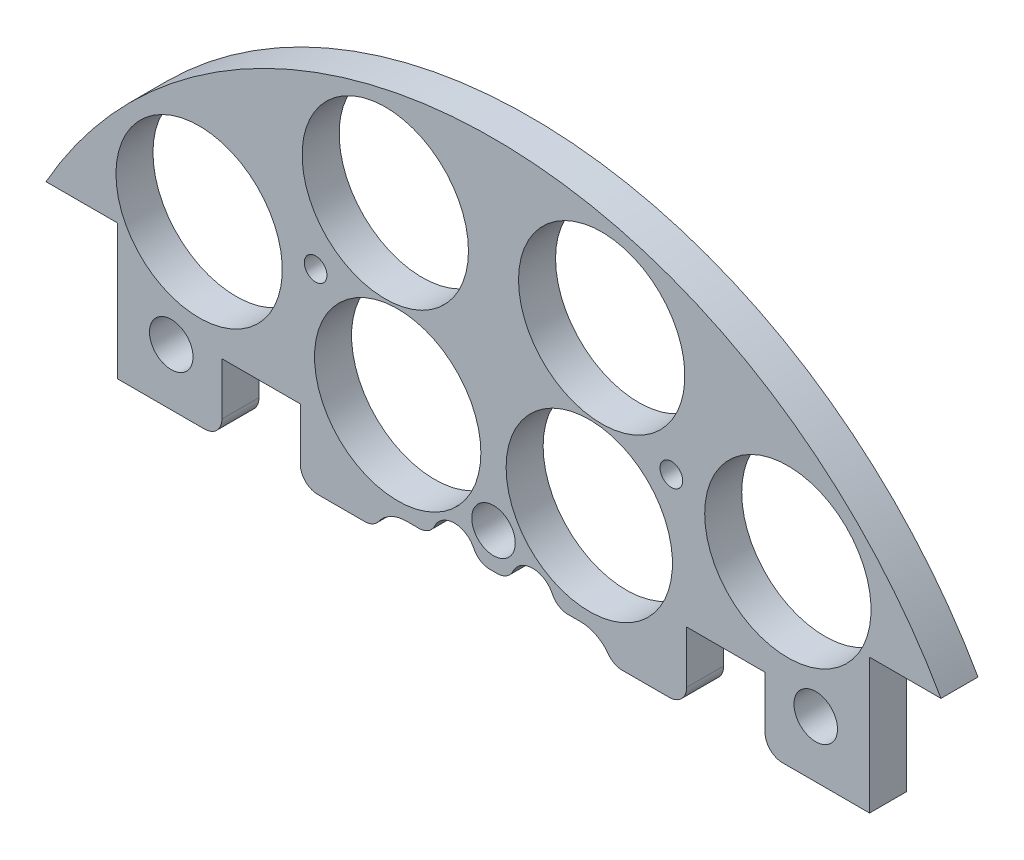
SolidWorks part; units mm, degrees
ref_plane "Front Plane" through (0, 0, 0) normal (0, 0, 1) x (1, 0, 0)
ref_plane "Top Plane" through (0, 0, 0) normal (0, 1, 0) x (1, 0, 0)
ref_plane "Right Plane" through (0, 0, 0) normal (1, 0, 0) x (0, 0, -1)
sketch "Sketch1" plane through (0, 0, 0) normal (0, 0, 1) x (1, 0, 0)
  line L0 (0, 0) -> (-82.1241, 0) construction
  line L1 (0, 0) -> (0, 95.6219) construction
  line L3 (-65.2538, 36.83) -> (-54.8398, 36.83)
  line L5 (-65.2538, -36.83) -> (-54.8398, -36.83)
  line L6 (-54.8398, 36.83) -> (-54.8398, -36.83)
  line L7 (65.2538, -36.83) -> (54.8398, -36.83)
  line L8 (65.2538, 36.83) -> (54.8398, 36.83)
  line L9 (54.8398, 36.83) -> (54.8398, -36.83)
  arc A0 (-65.2538, -36.83) -> (65.2538, -36.83) centre (0, 0) ccw
  circle A1 centre (-45.466, 11.049) radius 1.651
  circle A2 centre (-20.0673, 10.795) radius 1.651
  circle A3 centre (-20.0673, -10.795) radius 1.651
  circle A4 centre (-45.466, -11.049) radius 1.651
  circle A5 centre (45.466, -11.049) radius 1.651
  circle A6 centre (20.0673, -10.795) radius 1.651
  circle A7 centre (20.0673, 10.795) radius 1.651
  circle A8 centre (45.466, 11.049) radius 1.651
  arc A9 (65.2538, 36.83) -> (-65.2538, 36.83) centre (0, 0) ccw
  dimension "D2" = 3.302
  dimension "D3" = 3.302
  dimension "D4" = 25.4
  dimension "D5" = 10.795
  dimension "D10" = 45.466
  dimension "D6" = 73.66
  dimension "D7" = 10.414
  dimension "D8" = 74.93
  dimension "D9" = 74.93
  dimension "D11" = 36.83
extrude "Boss-Extrude2" add sketch "Sketch1" along normal blind 5.3975
sketch "Sketch2" plane through (0, 0, 5.3975) normal (0, 0, 1) x (1, 0, 0)
  line L0 (0, 68.58) -> (0, 55.88) construction
  line L1 (-9.525, 68.58) -> (9.525, 68.58)
  line L2 (-9.525, 68.58) -> (-9.525, 55.88)
  line L3 (-9.525, 55.88) -> (9.525, 55.88)
  line L4 (9.525, 68.58) -> (9.525, 55.88)
  line L5 (-9.525, 62.23) -> (9.525, 62.23) construction
  arc A0 (65.2538, 36.83) -> (-65.2538, 36.83) centre (0, 0) ccw construction
  circle A1 centre (-20.0673, 10.795) radius 1.651 construction
  circle A2 centre (20.0673, 10.795) radius 1.651 construction
  circle A3 centre (-6.731, 62.23) radius 1.143
  circle A4 centre (6.731, 62.23) radius 1.143
  dimension "D4" = 2.286
  dimension "D5" = 0
  dimension "D6" = 6.731
  dimension "D1" = 19.05
  dimension "D2" = 12.7
  dimension "D3" = 55.88
extrude "Cut-Extrude1" cut sketch "Sketch2" against normal through all contours A3 | A4
sketch "Sketch3" plane through (0, 0, 0) normal (0, 0, -1) x (-1, 0, 0)
  line L0 (0, 0) -> (0, -116.2908) construction
  line L1 (0, 0) -> (-153.8039, 0) construction
  arc A0 (65.2538, 36.83) -> (-65.2538, 36.83) centre (0, 0) ccw construction
  circle A4 centre (-42.926, -42.926) radius 12.1285
  circle A6 centre (13.97, -34.29) radius 12.1285
  circle A7 centre (13.97, 34.29) radius 12.1285
  circle A8 centre (-42.926, 42.926) radius 12.1285
  circle A11 centre (42.926, 42.926) radius 12.1285
  circle A12 centre (-13.97, 34.29) radius 12.1285
  circle A13 centre (-13.97, -34.29) radius 12.1285
  circle A14 centre (42.926, -42.926) radius 12.1285
  point P36 (0, 0)
  point P53 (0, 0)
  point P55 (0, 0)
  dimension "D1" = 42.926
  dimension "D3" = 42.926
  dimension "D4" = 24.257
  dimension "D5" = 34.29
  dimension "D6" = 13.97
extrude "Cut-Extrude2" cut sketch "Sketch3" against normal through all
sketch "Sketch4" plane through (0, 0, 0) normal (0, 0, -1) x (-1, 0, 0)
  line L1 (-15.7702, 56.3138) -> (12.7925, 56.3138)
  line L2 (-15.7702, 56.3138) -> (-15.7702, 67.9913)
  line L3 (-15.7702, 67.9913) -> (12.7925, 67.9913)
  line L4 (12.7925, 56.3138) -> (12.7925, 67.9913)
extrude "Boss-Extrude3" add sketch "Sketch4" against normal up to surface (5.3975 mm away) up to face at (-55.0545, -42.926, 5.3975)
sketch "Sketch5" plane through (0, 0, 0) normal (0, 0, -1) x (-1, 0, 0)
  line L1 (-113.3786, -90.442) -> (117.3207, -90.442)
  line L2 (-113.3786, -90.442) -> (-113.3786, 17.145)
  line L3 (-113.3786, 17.145) -> (117.3207, 17.145)
  line L4 (117.3207, -90.442) -> (117.3207, 17.145)
  circle A1 centre (20.0673, 10.795) radius 1.651 construction
  dimension "D1" = 6.35
extrude "Cut-Extrude3" cut sketch "Sketch5" against normal through all
sketch "Sketch6" plane through (0, 0, 0) normal (0, 0, -1) x (-1, 0, 0)
  line L0 (0, 0) -> (0, 74.93) construction
  line L1 (0, 0) -> (-15.5068, 57.8721) construction
  arc A0 (65.2538, 36.83) -> (-65.2538, 36.83) centre (0, 0) ccw construction
  circle A1 centre (-15.7776, 58.8828) radius 12.1285
  circle A3 centre (15.7776, 58.8828) radius 12.1285
  dimension "D1" = 24.257
  dimension "D2" = 0
  dimension "D4" = 60.96
  dimension "D3" = 15
extrude "Cut-Extrude4" cut sketch "Sketch6" against normal through all
extrude "Cut-Extrude55" cut sketch "Sketch57" against normal through all both and the other way through all
sketch "Sketch57" plane through (-29.8755, 133.1307, 31.75) normal (0, 0, 1) x (0.01, 0.9999, 0)
  line L0 (-132.614, -31.3134) -> (-132.614, 57.8454) construction
  line L1 (-132.614, -31.3134) -> (-222.516, -31.3134) construction
  circle A0 centre (-158.014, 14.4066) radius 3.175
  circle A1 centre (-173.254, -31.3134) radius 3.175
  circle A3 centre (-158.014, -77.0334) radius 3.175
  circle A4 centre (-107.214, -77.0334) radius 3.175
  circle A5 centre (-91.974, -31.3134) radius 3.175
  circle A6 centre (-107.214, 14.4066) radius 3.175
sketch "Sketch58" [suppressed] plane through (0, 0, 0) normal (0, 0, -1) x (-1, 0, 0)
  circle A0 centre (-46.082, 25.1518) radius 4.445
  circle A1 centre (-0.5167, 40.8482) radius 4.445
  circle A2 centre (45.3534, 26.0662) radius 4.445
  circle A3 centre (-46.082, 25.1518) radius 3.175 construction
  circle A4 centre (-0.5167, 40.8482) radius 3.175 construction
  circle A5 centre (45.3534, 26.0662) radius 3.175 construction
  dimension "D1" = 1.27
  dimension "D2" = 1.27
  dimension "D3" = 1.27
extrude "Boss-Extrude4" [suppressed] add sketch "Sketch58" against normal up to surface (6.35 mm away)
extrude "Cut-Extrude56" cut sketch "Sketch59" against normal through all both and the other way through all
sketch "Sketch59" plane through (31.3134, 132.614, -19.05) normal (0, 0, -1) x (0, 1, 0)
  line L0 (-132.614, -31.3134) -> (-132.614, 57.8454) construction
  line L1 (-132.614, -31.3134) -> (-222.516, -31.3134) construction
  circle A0 centre (-158.014, 14.4066) radius 3.175
  circle A1 centre (-173.254, -31.3134) radius 3.175
  circle A3 centre (-158.014, -77.0334) radius 3.175
  circle A4 centre (-107.214, -77.0334) radius 3.175
  circle A5 centre (-91.974, -31.3134) radius 3.175
  circle A6 centre (-107.214, 14.4066) radius 3.175
extrude "Cut-Extrude60" cut sketch "Sketch63" against normal blind 29.21
sketch "Sketch63" plane through (31.3134, 132.559, -15.875) normal (0, 0, -1) x (0, 1, 0)
  line L0 (-132.559, -31.3134) -> (6.1626, -31.3134) construction
  line L2 (-132.559, -31.3134) -> (-132.559, -122.6589) construction
  circle A0 centre (-190.979, 2.9766) radius 1.651
  circle A2 centre (-154.784, -31.3134) radius 1.651
  circle A3 centre (-190.979, -65.6034) radius 1.651
  circle A4 centre (-110.334, -31.3134) radius 1.651
  circle A5 centre (-74.139, -65.6034) radius 1.651
  circle A6 centre (-74.139, 2.9766) radius 1.651
extrude "Cut-Extrude151" cut sketch "Sketch155" against normal blind 29.21
sketch "Sketch155" plane through (-31.3134, 132.559, 15.875) normal (0, 0, 1) x (0, 1, 0)
  line L0 (-143.7712, -34.3645) -> (6.1626, -34.3645) construction
  line L2 (-143.7712, -34.3645) -> (-143.7712, -122.6589) construction
  circle A0 centre (-202.1912, -0.0745) radius 1.651
  circle A2 centre (-165.9962, -34.3645) radius 1.651
  circle A3 centre (-202.1912, -68.6545) radius 1.651
  circle A4 centre (-121.5462, -34.3645) radius 1.651
  circle A5 centre (-85.3512, -68.6545) radius 1.651
  circle A6 centre (-85.3512, -0.0745) radius 1.651
sketch "Sketch156" plane through (0, 0, 0) normal (0, 0, -1) x (-1, 0, 0)
  line L0 (54.8398, 17.145) -> (-54.8398, 17.145) construction
  line L1 (39.5998, 17.145) -> (28.1698, 17.145)
  line L2 (39.5998, 17.145) -> (39.5998, 27.305)
  line L3 (39.5998, 27.305) -> (28.1698, 27.305)
  line L4 (28.1698, 17.145) -> (28.1698, 27.305)
  line L5 (54.8398, 36.83) -> (54.8398, 17.145) construction
  line L6 (-28.1698, 17.145) -> (-39.5998, 17.145)
  line L7 (-28.1698, 17.145) -> (-28.1698, 27.305)
  line L8 (-28.1698, 27.305) -> (-39.5998, 27.305)
  line L9 (-39.5998, 17.145) -> (-39.5998, 27.305)
  line L10 (0, 8.076) -> (0, 81.5725) construction
  dimension "D1" = 10.16
  dimension "D2" = 11.43
  dimension "D3" = 15.24
extrude "Cut-Extrude152" cut sketch "Sketch156" against normal through all
extrude "Cut-Extrude208" cut sketch "Sketch212" against normal blind 97.79
sketch "Sketch212" plane through (30.092, 4.0835, -19.2405) normal (0, 0, -1) x (-1, 0, 0)
  line L0 (30.092, -29.4835) -> (30.092, 6.2385) construction
  circle A0 centre (4.1544, -49.7288) radius 1.651
  circle A4 centre (56.0296, -49.7288) radius 1.651
  circle A5 centre (4.1544, 41.3825) radius 1.651
  circle A9 centre (56.0296, 41.3825) radius 1.651
extrude "Cut-Extrude262" cut sketch "Sketch266" against normal blind 48.768 and the other way blind 103.378
sketch "Sketch266" plane through (30.092, 4.0835, 16.891) normal (0, 0, -1) x (-1, 0, 0)
  line L0 (30.092, -4.0835) -> (148.6336, -4.0835) construction
  line L1 (30.092, -4.0835) -> (30.092, 90.452) construction
  circle A0 centre (-16.898, 21.3165) radius 3.175
  circle A1 centre (77.082, 21.3165) radius 3.175
  circle A2 centre (30.092, 21.3165) radius 3.175
  circle A4 centre (77.082, -29.4835) radius 3.175
  circle A5 centre (30.092, -29.4835) radius 3.175
  circle A6 centre (-16.898, -29.4835) radius 3.175
sketch "Sketch159" plane through (0, 0, 0) normal (0, 0, -1) x (-1, 0, 0)
  line L0 (0, 0) -> (0, -30.2794) construction
  line L1 (12.7, 20.24) -> (8.889, 20.24)
  line L2 (7.7, 15.24) -> (-7.7, 15.24)
  line L3 (-8.889, 20.24) -> (-12.7, 20.24)
  line L4 (2.541, 20.24) -> (-2.541, 20.24)
  arc A0 (7.7, 15.24) -> (12.7, 20.24) centre (12.7, 15.24) ccw
  arc A1 (-7.7, 15.24) -> (-12.7, 20.24) centre (-12.7, 15.24) cw
  arc A2 (8.889, 20.24) -> (2.541, 20.24) centre (5.715, 20.32) ccw
  arc A3 (-2.541, 20.24) -> (-8.889, 20.24) centre (-5.715, 20.32) ccw
  dimension "D1" = 10
  dimension "D4" = 6.35
  dimension "D5" = 6.35
  dimension "D2" = 12.7
  dimension "D3" = 15.24
  dimension "D6" = 11.43
  dimension "D7" = 5.715
  dimension "D8" = 20.32
extrude "Cut-Extrude155" cut sketch "Sketch159" against normal blind 26.162
fillet "Fillet1" radius 2.54 10 edges at (39.5998, 17.145, 2.6987) (28.1698, 17.145, 2.6987) (17.3229, 17.145, 2.6987) (8.889, 20.24, 2.6988) (2.541, 20.24, 2.6988) (-2.541, 20.24, 2.6988) (-8.889, 20.24, 2.6988) (-17.3229, 17.145, 2.6987) (-28.1698, 17.145, 2.6987) (-39.5998, 17.145, 2.6987)
